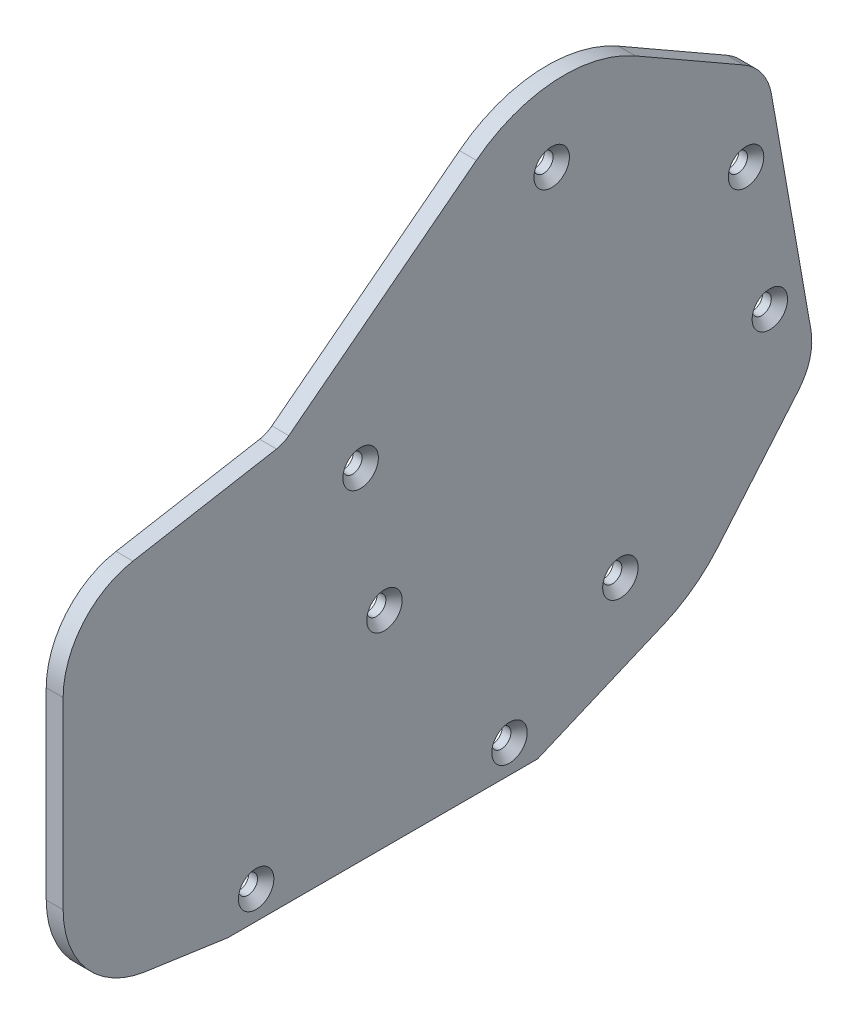
SolidWorks part; units mm, degrees
material "Thornel VCB-20 Carbon Cloth"
ref_plane "Front Plane" through (0, 0, 0) normal (0, 0, 1) x (1, 0, 0)
ref_plane "Top Plane" through (0, 0, 0) normal (0, 1, 0) x (1, 0, 0)
ref_plane "Right Plane" through (0, 0, 0) normal (1, 0, 0) x (0, 0, -1)
ref_plane "Plane1" through (29, 0, 0) normal (1, 0, 0) x (0, 0, -1)
sketch "Sketch2" plane through (29, 0, 0) normal (1, 0, 0) x (0, 0, -1)
  line L4 (-16.6915, 108.8163) -> (16.6101, 134.5066)
  line L6 (69.0263, 118.4582) -> (76.0353, 78.7081)
  line L8 (-27.5, 37) -> (27.5, 37)
  line L9 (27.5, 37) -> (49.9564, 46.5241)
  line L10 (68.8961, 119.1968) -> (76.1656, 77.9695) construction
  line L11 (64.1472, 125.3998) -> (44.8568, 136.4454)
  line L12 (59.4754, 53.5392) -> (73.8247, 70.5164)
  line L13 (-27.5, 37) -> (-42.1838, 39.1068)
  line L14 (-18.8773, 107.8511) -> (-44.3742, 103.3553)
  line L15 (-56.7694, 88.5832) -> (-56.7694, 55.9345)
  line L16 (-42.1957, 104.2472) -> (-19.5451, 108.2411) construction
  circle A0 centre (40, 70) radius 22.5 construction
  circle A4 centre (-22.5, 42) radius 3 construction
  circle A5 centre (22.5, 42) radius 3 construction
  circle A6 centre (32.1858, 114.3163) radius 22.5 construction
  circle A7 centre (40, 70) radius 22.5 construction
  circle A8 centre (32.1858, 114.3163) radius 22.5 construction
  arc A12 (49.9564, 46.5241) -> (59.4754, 53.5392) centre (40, 70) ccw
  arc A13 (44.8568, 136.4454) -> (16.6101, 134.5066) centre (32.1858, 114.3163) ccw
  arc A14 (69.0263, 118.4582) -> (64.1472, 125.3998) centre (59.1782, 116.7217) ccw
  arc A15 (76.0353, 78.7081) -> (73.8247, 70.5164) centre (66.1872, 76.9716) cw
  arc A16 (-56.7694, 55.9345) -> (-42.1838, 39.1068) centre (-39.7694, 55.9345) ccw
  circle A17 centre (-39.7694, 55.9345) radius 14 construction
  arc A19 (-16.6915, 108.8163) -> (-18.8773, 107.8511) centre (-19.7456, 112.7751) cw
  arc A20 (-44.3742, 103.3553) -> (-56.7694, 88.5832) centre (-41.7694, 88.5832) ccw
  arc A21 (-15.3585, 110.4119) -> (-19.7366, 103.5685) centre (-13.8278, 104.6104) ccw construction
  dimension "D1" = 6
  dimension "D2" = 3
  dimension "D3" = 3
  dimension "D5" = 5
  dimension "D6" = 15
  dimension "D7" = 10
  dimension "D4" = 0.5
extrude "Boss-Extrude1" add sketch "Sketch2" along normal blind 3
hole_wizard "CSK for M3 Flat Head Machine Screw1" positions "Sketch3" profile "Sketch4" countersink size "M3" standard "ANSI Metric" end condition through all
sketch "Sketch3" plane through (32, 0, 0) normal (1, 0, 0) x (0, 0, -1)
  point P0 (64.5066, 109.5379)
  point P3 (68.7373, 85.5447)
  point P6 (-3.9375, 97.4693)
  point P9 (0.2931, 73.4761)
  point P12 (42.1966, 57.5422)
  point P15 (29.9892, 126.7742)
  point P19 (-22.5, 42)
  point P22 (22.5, 42)
sketch "Sketch4" plane through (32, 109.5379, -64.5066) normal (0, 1, 0) x (0, 0, -1)
  line L0 (0, 0) -> (0, 3)
  line L1 (0, 3) -> (1.7, 3)
  line L2 (1.7, 3) -> (1.7, 1.45)
  line L3 (1.7, 1.45) -> (3.15, 0)
  line L5 (3.15, 0) -> (0, 0)
  line L6 (-1.7, 1.45) -> (-3.15, 0) construction
  line L11 (0, -6.35) -> (0, 107.95) construction
  dimension "Thru Hole Dia." = 3.4
  dimension "Thru Hole Depth" = 3
  dimension "Near C'Sink Dia." = 6.3
  dimension "Near C'Sink Angle" = 90
